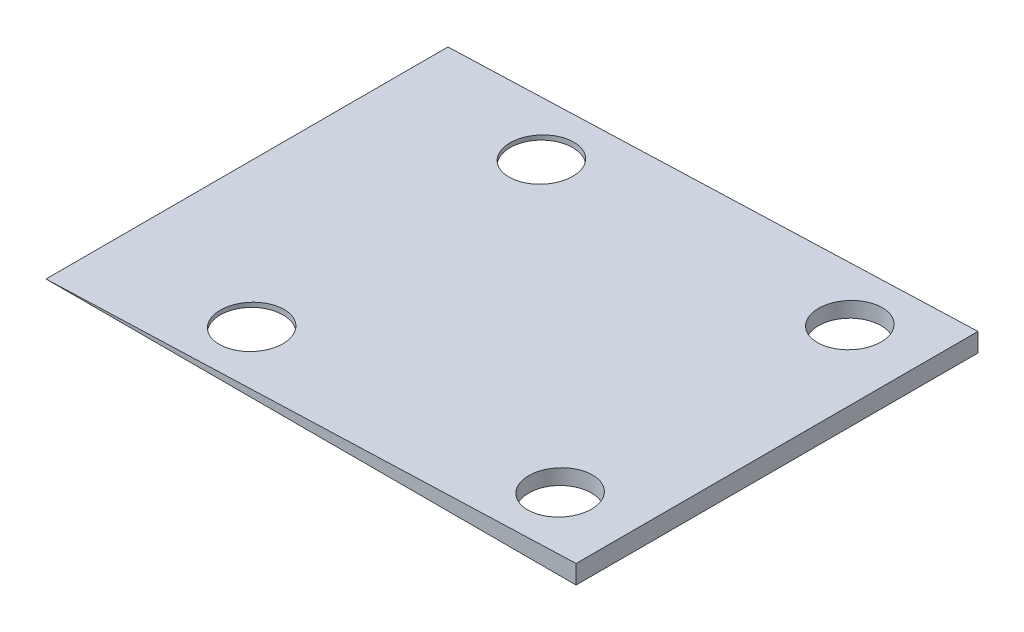
SolidWorks part; units mm, degrees
ref_plane "Front Plane" through (0, 0, 0) normal (0, 0, 1) x (1, 0, 0)
ref_plane "Top Plane" through (0, 0, 0) normal (0, 1, 0) x (1, 0, 0)
ref_plane "Right Plane" through (0, 0, 0) normal (1, 0, 0) x (0, 0, -1)
sketch "Sketch1" plane through (0, 0, 0) normal (0, 0, 1) x (1, 0, 0)
  line L0 (0, 0) -> (56.71, 0)
  line L1 (56.71, 0) -> (56.71, 2)
  line L2 (56.71, 2) -> (0, 0)
  dimension "D1" = 56.71
  dimension "D2" = 2
extrude "Boss-Extrude1" add sketch "Sketch1" along normal blind 43
sketch "Sketch2" plane through (0, 0, 0) normal (0, -1, 0) x (1, 0, 0)
  circle A0 centre (49, 6) radius 3.35 construction
  circle A1 centre (49, 37) radius 3.35 construction
  circle A2 centre (16, 37) radius 3.35 construction
  circle A3 centre (16, 6) radius 3.35 construction
  circle A4 centre (49, 6) radius 3.35
  circle A5 centre (49, 37) radius 3.35
  circle A6 centre (16, 37) radius 3.35
  circle A7 centre (16, 6) radius 3.35
extrude "Cut-Extrude1" cut sketch "Sketch2" against normal up to surface (1.7281 mm away)
